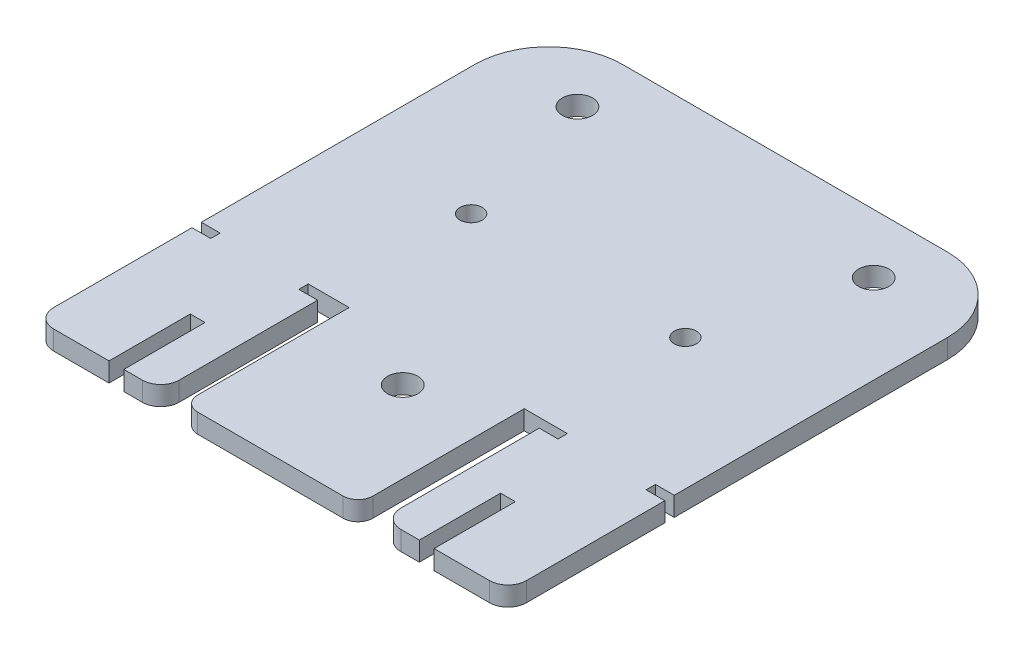
SolidWorks part; units mm, degrees
ref_plane "Front Plane" through (0, 0, 0) normal (0, 0, 1) x (1, 0, 0)
ref_plane "Top Plane" through (0, 0, 0) normal (0, 1, 0) x (1, 0, 0)
ref_plane "Right Plane" through (0, 0, 0) normal (1, 0, 0) x (0, 0, -1)
sketch "Sketch1" plane through (0, 0, 0) normal (0, 1, 0) x (1, 0, 0)
  line L0 (11.7, -23.5) -> (32, -23.5)
  line L1 (-32, -23.5) -> (-12, -23.5)
  line L2 (-32, -23.5) -> (-32, 13.5)
  line L3 (-22, 23.5) -> (22, 23.5)
  line L4 (32, -23.5) -> (32, 13.5)
  line L5 (-32, -23.5) -> (32, 23.5) construction
  line L6 (-32, 23.5) -> (32, -23.5) construction
  line L8 (-12, -23.5) -> (-12, -46)
  line L9 (-12, -46) -> (11.7, -46)
  line L10 (11.7, -23.5) -> (11.7, -46)
  arc A0 (-32, 13.5) -> (-22, 23.5) centre (-22, 13.5) cw
  arc A1 (32, 13.5) -> (22, 23.5) centre (22, 13.5) ccw
  point P0 (0, 0)
  dimension "D6" = 10
  dimension "D7" = 10
  dimension "D1" = 64
  dimension "D2" = 47
  dimension "D3" = 20
  dimension "D4" = 23.7
  dimension "D5" = 22.5
extrude "Main Body" add sketch "Sketch1" along normal blind 2.6
sketch "Sketch2" plane through (0, 2.6, 0) normal (0, 1, 0) x (1, 0, 0)
  line L0 (22, 23.5) -> (-22, 23.5) construction
  line L1 (-32, 13.5) -> (-32, -23.5) construction
  line L2 (0, 0) -> (0, 23.5) construction
  line L3 (32, -23.5) -> (32, 13.5) construction
  line L4 (0.7, -31) -> (0.7, -32.3) construction
  line L5 (0.7, -32.3) -> (14.26, -32.3) construction
  line L6 (-12, -23.5) -> (-12, -46) construction
  line L7 (14.26, -32.3) -> (14.26, -4.25) construction
  line L8 (-14.74, -4.25) -> (-16.24, -4.25) construction
  line L9 (14.26, -4.25) -> (15.76, -4.25) construction
  circle A0 centre (-20.1, 15.5) radius 2.05
  circle A1 centre (20, 15.5) radius 2.05
  circle A3 centre (-14.74, -4.25) radius 1.5
  circle A4 centre (14.26, -4.25) radius 1.5
  circle A6 centre (0.7, -28.95) radius 2.05
  dimension "D1" = 4.1
  dimension "D4" = 4.1
  dimension "D7" = 29
  dimension "D8" = 3
  dimension "D9" = 3
  dimension "D10" = 13.56
  dimension "D11" = 4.1
  dimension "D2" = 8
  dimension "D3" = 11.9
  dimension "D5" = 8
  dimension "D6" = 12
  dimension "D12" = 28.05
  dimension "D13" = 1.3
  dimension "D20" = 12.7
  dimension "D21" = 44.45
extrude "Screw holes" cut sketch "Sketch2" against normal through all both and the other way through all
fillet "Main lower body Fillet" radius 2 2 edges at (11.7, 1.3, 46) (-12, 1.3, 46)
sketch "Sketch4" plane through (0, 2.6, 0) normal (0, 1, 0) x (1, 0, 0)
  line L1 (-32, -23.5) -> (-15, -23.5)
  line L2 (-32, -23.5) -> (-32, -21)
  line L3 (-32, -21) -> (-15, -21)
  line L4 (-15, -23.5) -> (-15, -21)
  line L5 (32, -23.5) -> (15, -23.5)
  line L6 (32, -23.5) -> (32, -21)
  line L7 (32, -21) -> (15, -21)
  line L8 (15, -23.5) -> (15, -21)
  dimension "D1" = 2.5
  dimension "D2" = 2.5
  dimension "D3" = 17
  dimension "D4" = 17
sketch "Sketch5" plane through (0, 0, 23.5) normal (0, 0, 1) x (1, 0, 0)
  line L0 (-32, 0) -> (-12, 0) construction
  line L1 (-32, 2.6) -> (-15, 2.6)
  line L2 (-32, 2.6) -> (-32, 0)
  line L3 (-32, 0) -> (-15, 0)
  line L4 (-15, 2.6) -> (-15, 0)
  line L5 (11.7, 0) -> (32, 0) construction
  line L6 (32, 2.6) -> (15, 2.6)
  line L7 (32, 2.6) -> (32, 0)
  line L8 (32, 0) -> (15, 0)
  line L9 (15, 2.6) -> (15, 0)
  dimension "D1" = 17
  dimension "D2" = 17
extrude "Boss-Extrude1" add sketch "Sketch5" along normal blind 22.5
sketch "Sketch6" plane through (0, 2.6, 0) normal (0, 1, 0) x (1, 0, 0)
  line L0 (-15, -46) -> (-32, -46) construction
  line L1 (-20, -46) -> (-22, -46)
  line L2 (-20, -46) -> (-20, -35)
  line L3 (-20, -35) -> (-22, -35)
  line L4 (-22, -46) -> (-22, -35)
  line L5 (32, -46) -> (15, -46) construction
  line L6 (22, -46) -> (20, -46)
  line L7 (22, -46) -> (22, -35)
  line L8 (22, -35) -> (20, -35)
  line L9 (20, -46) -> (20, -35)
  line L10 (-32, 13.5) -> (-32, -46) construction
  line L11 (32, -46) -> (32, 13.5) construction
  point P16 (21, -35)
  dimension "D1" = 12
  dimension "D2" = 12
  dimension "D3" = 10
  dimension "D4" = 10
  dimension "D5" = 11
  dimension "D6" = 11
extrude "Cut-Extrude1" cut sketch "Sketch6" against normal blind 22.5
fillet "Fillet2" radius 2.5 4 edges at (-32, 1.3, 46) (-15, 1.3, 46) (15, 1.3, 46) (32, 1.3, 46)
sketch "Sketch7" plane through (0, 2.6, 0) normal (0, 1, 0) x (1, 0, 0)
  line L0 (32, -23.5) -> (15, -23.5) construction
  line L1 (-32, -23.5) -> (-29.46, -23.5)
  line L2 (-32, -23.5) -> (-32, -24.77)
  line L3 (-32, -24.77) -> (-29.46, -24.77)
  line L4 (-29.46, -23.5) -> (-29.46, -24.77)
  line L5 (32, -23.5) -> (29.46, -23.5)
  line L6 (32, -23.5) -> (32, -24.77)
  line L7 (32, -24.77) -> (29.46, -24.77)
  line L8 (29.46, -23.5) -> (29.46, -24.77)
  line L10 (-15, -23.5) -> (-17.54, -23.5)
  line L11 (-15, -23.5) -> (-15, -24.77)
  line L12 (-15, -24.77) -> (-17.54, -24.77)
  line L13 (-17.54, -23.5) -> (-17.54, -24.77)
  line L14 (15, -23.5) -> (17.54, -23.5)
  line L15 (15, -23.5) -> (15, -24.77)
  line L16 (15, -24.77) -> (17.54, -24.77)
  line L17 (17.54, -23.5) -> (17.54, -24.77)
  dimension "D1" = 2.54
  dimension "D2" = 2.54
  dimension "D3" = 1.27
  dimension "D4" = 1.27
  dimension "D5" = 2.54
  dimension "D6" = 2.54
  dimension "D7" = 1.27
  dimension "D8" = 1.27
extrude "Cut-Extrude2" cut sketch "Sketch7" against normal through all
sketch "Sketch8" plane through (0, 2.6, 0) normal (0, 1, 0) x (1, 0, 0)
  line L0 (-32, -28.95) -> (-32, -46) construction
  line L1 (-32, -24.77) -> (-32, -43.5) construction
  line L2 (0.7, -28.95) -> (0.7, -46)
  line L4 (-32, -46) -> (0.7, -46) construction
  circle A0 centre (0.7, -28.95) radius 2.05
  dimension "D1" = 32.7
  dimension "D2" = 17.05
